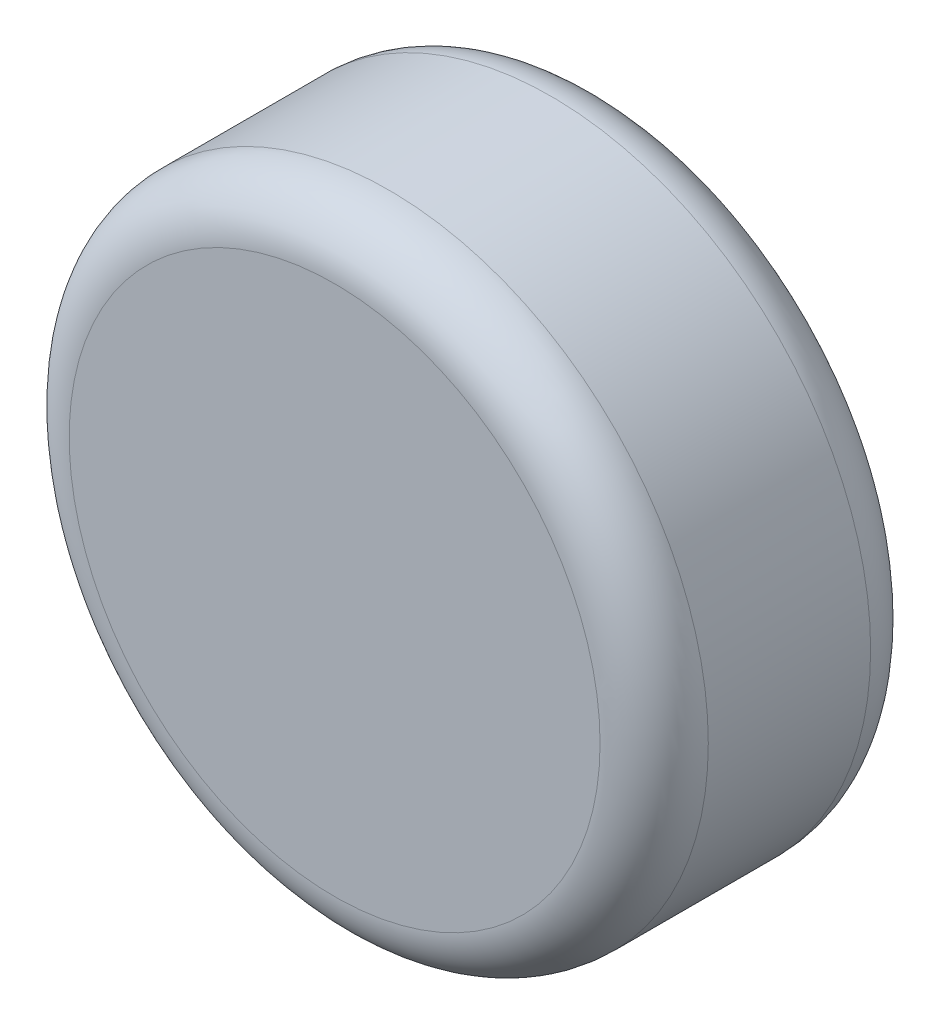
SolidWorks part; units mm, degrees
ref_plane "Front Plane" through (0, 0, 0) normal (0, 0, 1) x (1, 0, 0)
ref_plane "Top Plane" through (0, 0, 0) normal (0, 1, 0) x (1, 0, 0)
ref_plane "Right Plane" through (0, 0, 0) normal (1, 0, 0) x (0, 0, -1)
sketch "Sketch1" plane through (39.6132, -21.5957, -219.5051) normal (0, 0, 1) x (1, 0, 0)
  circle A0 centre (23.6312, 58.2787) radius 15
  dimension "D1" = 30
extrude "Boss-Extrude1" add sketch "Sketch1" along normal blind 12.7 contours A0
fillet "Fillet1" radius 2.54 2 edges at (78.2443, 36.6829, -219.5051) (78.2443, 36.6829, -206.8051)
